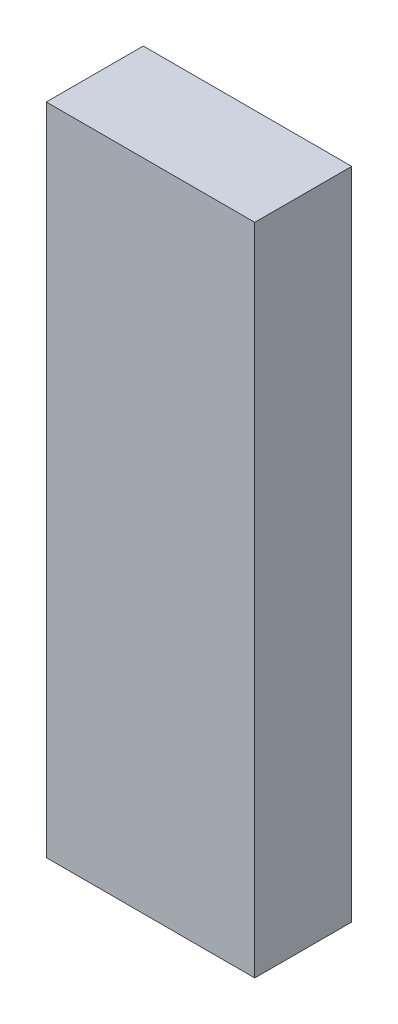
SolidWorks part; units mm, degrees
material "5200电池"
ref_plane "前视基准面" through (0, 0, 0) normal (0, 0, 1) x (1, 0, 0)
ref_plane "上视基准面" through (0, 0, 0) normal (0, 1, 0) x (1, 0, 0)
ref_plane "右视基准面" through (0, 0, 0) normal (1, 0, 0) x (0, 0, -1)
other "Configuration Table"
sketch "草图1" plane through (0, 0, 0) normal (0, 0, 1) x (1, 0, 0)
  line L1 (140.6897, -45.5725) -> (183.6897, -45.5725)
  line L2 (140.6897, -45.5725) -> (140.6897, 89.4275)
  line L3 (140.6897, 89.4275) -> (183.6897, 89.4275)
  line L4 (183.6897, -45.5725) -> (183.6897, 89.4275)
  dimension "D1" = 135
  dimension "D2" = 43
extrude "凸台-拉伸1" add sketch "草图1" along normal blind 20
